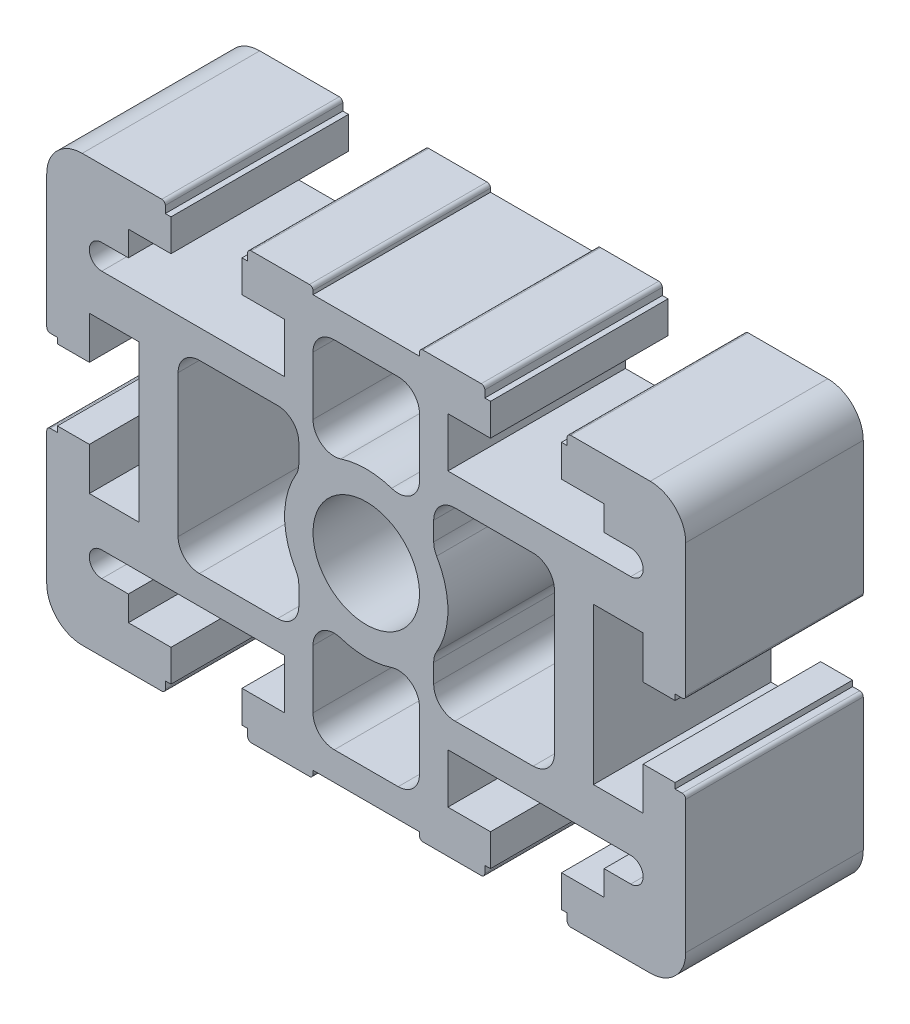
SolidWorks part; units mm, degrees
material "1060 Alloy"
ref_plane "Front" through (0, 0, 0) normal (0, 0, 1) x (1, 0, 0)
ref_plane "Top" through (0, 0, 0) normal (0, 1, 0) x (1, 0, 0)
ref_plane "Right" through (0, 0, 0) normal (1, 0, 0) x (0, 0, -1)
ref_plane "Plane1" through (0, 0, 0) normal (0, 0, 1) x (1, 0, 0)
sketch "Sketch1" plane through (0, 0, 0) normal (0, 0, 1) x (1, 0, 0)
  line L0 (7.4988, -13.7844) -> (7.4988, -22)
  line L1 (4.4988, -25) -> (-4.4988, -25)
  line L2 (-7.4988, -22) -> (-7.4988, -13.7844)
  line L3 (-7.4988, 13.7844) -> (-7.4988, 22)
  line L4 (-4.4988, 25) -> (4.4988, 25)
  line L5 (7.4988, 22) -> (7.4988, 13.7844)
  line L6 (26.4988, 10) -> (26.4988, -10)
  line L7 (23.4988, -13) -> (12.4988, -13)
  line L8 (9.4988, -10) -> (9.4988, -7.3505)
  line L9 (9.4988, 7.3505) -> (9.4988, 10)
  line L10 (12.4988, 13) -> (23.4988, 13)
  line L11 (-9.4988, -7.3505) -> (-9.4988, -10)
  line L12 (-12.4988, -13) -> (-23.4988, -13)
  line L13 (-26.4988, -10) -> (-26.4988, 10)
  line L14 (-23.4988, 13) -> (-12.4988, 13)
  line L15 (-9.4988, 10) -> (-9.4988, 7.3505)
  line L16 (28.7987, -30) -> (39.9987, -30)
  line L17 (44.9987, -25) -> (44.9987, -6.3)
  line L18 (44.4987, -5.8) -> (43.4987, -5.8)
  line L19 (43.4987, -5.8) -> (43.4987, -5)
  line L20 (43.4987, -5) -> (38.9987, -5)
  line L21 (38.9987, -5) -> (38.9987, -11)
  line L22 (38.9987, -11) -> (31.9987, -11)
  line L23 (31.9987, -11) -> (31.9987, 11)
  line L24 (31.9987, 11) -> (38.9987, 11)
  line L25 (38.9987, 11) -> (38.9987, 5)
  line L26 (38.9987, 5) -> (43.4987, 5)
  line L27 (43.4987, 5) -> (43.4987, 5.8)
  line L28 (43.4987, 5.8) -> (44.4987, 5.8)
  line L29 (44.9987, 6.3) -> (44.9987, 25)
  line L30 (39.9987, 30) -> (28.7987, 30)
  line L31 (28.2987, 29.5) -> (28.2987, 28.5)
  line L32 (28.2987, 28.5) -> (27.4987, 28.5)
  line L33 (27.4987, 28.5) -> (27.4987, 24)
  line L34 (27.4987, 24) -> (33.4987, 24)
  line L35 (33.4987, 24) -> (33.4987, 20.5)
  line L36 (33.4987, 20.5) -> (37.2511, 20.5)
  line L37 (37.2511, 17) -> (11.4988, 17)
  line L38 (11.4988, 17) -> (11.4988, 24)
  line L39 (11.4988, 24) -> (17.4988, 24)
  line L40 (17.4988, 24) -> (17.4988, 28.5)
  line L41 (17.4988, 28.5) -> (16.6988, 28.5)
  line L42 (16.6988, 28.5) -> (16.6988, 29.5)
  line L43 (16.1988, 30) -> (8, 30)
  line L44 (7.5, 29.5) -> (7.5, 29)
  line L45 (7.5, 29) -> (-7.5, 29)
  line L46 (-7.5, 29) -> (-7.5, 29.5)
  line L47 (-8, 30) -> (-16.1988, 30)
  line L48 (-16.6988, 29.5) -> (-16.6988, 28.5)
  line L49 (-16.6988, 28.5) -> (-17.4988, 28.5)
  line L50 (-17.4988, 28.5) -> (-17.4988, 24)
  line L51 (-17.4988, 24) -> (-11.4988, 24)
  line L52 (-11.4988, 24) -> (-11.4988, 17)
  line L53 (-11.4988, 17) -> (-37.2511, 17)
  line L54 (-37.2511, 20.5) -> (-33.4987, 20.5)
  line L55 (-33.4987, 20.5) -> (-33.4987, 24)
  line L56 (-33.4987, 24) -> (-27.4987, 24)
  line L57 (-27.4987, 24) -> (-27.4987, 28.5)
  line L58 (-27.4987, 28.5) -> (-28.2987, 28.5)
  line L59 (-28.2987, 28.5) -> (-28.2987, 29.5)
  line L60 (-28.7987, 30) -> (-39.9987, 30)
  line L61 (-44.9987, 25) -> (-44.9987, 6.3)
  line L62 (-44.4987, 5.8) -> (-43.4987, 5.8)
  line L63 (-43.4987, 5.8) -> (-43.4987, 5)
  line L64 (-43.4987, 5) -> (-38.9987, 5)
  line L65 (-38.9987, 5) -> (-38.9987, 11)
  line L66 (-38.9987, 11) -> (-31.9987, 11)
  line L67 (-31.9987, 11) -> (-31.9987, -11)
  line L68 (-31.9987, -11) -> (-38.9987, -11)
  line L69 (-38.9987, -11) -> (-38.9987, -5)
  line L70 (-38.9987, -5) -> (-43.4987, -5)
  line L71 (-43.4987, -5) -> (-43.4987, -5.8)
  line L72 (-43.4987, -5.8) -> (-44.4987, -5.8)
  line L73 (-44.9987, -6.3) -> (-44.9987, -25)
  line L74 (-39.9987, -30) -> (-28.7987, -30)
  line L75 (-28.2987, -29.5) -> (-28.2987, -28.5)
  line L76 (-28.2987, -28.5) -> (-27.4987, -28.5)
  line L77 (-27.4987, -28.5) -> (-27.4987, -24)
  line L78 (-27.4987, -24) -> (-33.4987, -24)
  line L79 (-33.4987, -24) -> (-33.4987, -20.5)
  line L80 (-33.4987, -20.5) -> (-37.2511, -20.5)
  line L81 (-37.2511, -17) -> (-11.4988, -17)
  line L82 (-11.4988, -17) -> (-11.4988, -24)
  line L83 (-11.4988, -24) -> (-17.4988, -24)
  line L84 (-17.4988, -24) -> (-17.4988, -28.5)
  line L85 (-17.4988, -28.5) -> (-16.6988, -28.5)
  line L86 (-16.6988, -28.5) -> (-16.6988, -29.5)
  line L87 (-16.1988, -30) -> (-8, -30)
  line L88 (-7.5, -29.5) -> (-7.5, -29)
  line L89 (-7.5, -29) -> (7.5, -29)
  line L90 (7.5, -29) -> (7.5, -29.5)
  line L91 (8, -30) -> (16.1988, -30)
  line L92 (16.6988, -29.5) -> (16.6988, -28.5)
  line L93 (16.6988, -28.5) -> (17.4988, -28.5)
  line L94 (17.4988, -28.5) -> (17.4988, -24)
  line L95 (17.4988, -24) -> (11.4988, -24)
  line L96 (11.4988, -24) -> (11.4988, -17)
  line L97 (11.4988, -17) -> (37.2511, -17)
  line L98 (37.2511, -20.5) -> (33.4987, -20.5)
  line L99 (33.4987, -20.5) -> (33.4987, -24)
  line L100 (33.4987, -24) -> (27.4987, -24)
  line L101 (27.4987, -24) -> (27.4987, -28.5)
  line L102 (27.4987, -28.5) -> (28.2987, -28.5)
  line L103 (28.2987, -28.5) -> (28.2987, -29.5)
  circle A0 centre (0, 0) radius 7.5
  arc A1 (3.568, -10.9325) -> (7.4988, -13.7844) centre (4.4988, -13.7844) cw
  arc A2 (7.4988, -22) -> (4.4988, -25) centre (4.4988, -22) cw
  arc A3 (-4.4988, -25) -> (-7.4988, -22) centre (-4.4988, -22) cw
  arc A4 (-7.4988, -13.7844) -> (-3.568, -10.9325) centre (-4.4988, -13.7844) cw
  arc A5 (-3.568, -10.9325) -> (3.568, -10.9325) centre (0, 0) ccw
  arc A6 (-3.568, 10.9325) -> (-7.4988, 13.7844) centre (-4.4988, 13.7844) cw
  arc A7 (-7.4988, 22) -> (-4.4988, 25) centre (-4.4988, 22) cw
  arc A8 (4.4988, 25) -> (7.4988, 22) centre (4.4988, 22) cw
  arc A9 (7.4988, 13.7844) -> (3.568, 10.9325) centre (4.4988, 13.7844) cw
  arc A10 (3.568, 10.9325) -> (-3.568, 10.9325) centre (0, 0) ccw
  arc A11 (26.4988, -10) -> (23.4988, -13) centre (23.4988, -10) cw
  arc A12 (12.4988, -13) -> (9.4988, -10) centre (12.4988, -10) cw
  arc A13 (9.4988, -7.3505) -> (9.9128, -5.8297) centre (12.4988, -7.3505) cw
  arc A14 (9.9128, -5.8297) -> (9.9128, 5.8297) centre (0, 0) ccw
  arc A15 (9.9128, 5.8297) -> (9.4988, 7.3505) centre (12.4988, 7.3505) cw
  arc A16 (9.4988, 10) -> (12.4988, 13) centre (12.4988, 10) cw
  arc A17 (23.4988, 13) -> (26.4988, 10) centre (23.4988, 10) cw
  arc A18 (-9.9128, -5.8297) -> (-9.4988, -7.3505) centre (-12.4988, -7.3505) cw
  arc A19 (-9.4988, -10) -> (-12.4988, -13) centre (-12.4988, -10) cw
  arc A20 (-23.4988, -13) -> (-26.4988, -10) centre (-23.4988, -10) cw
  arc A21 (-26.4988, 10) -> (-23.4988, 13) centre (-23.4988, 10) cw
  arc A22 (-12.4988, 13) -> (-9.4988, 10) centre (-12.4988, 10) cw
  arc A23 (-9.4988, 7.3505) -> (-9.9128, 5.8297) centre (-12.4988, 7.3505) cw
  arc A24 (-9.9128, 5.8297) -> (-9.9128, -5.8297) centre (0, 0) ccw
  arc A25 (28.2987, -29.5) -> (28.7987, -30) centre (28.7987, -29.5) ccw
  arc A26 (39.9987, -30) -> (44.9987, -25) centre (39.9987, -25) ccw
  arc A27 (44.9987, -6.3) -> (44.4987, -5.8) centre (44.4987, -6.3) ccw
  arc A28 (44.4987, 5.8) -> (44.9987, 6.3) centre (44.4987, 6.3) ccw
  arc A29 (44.9987, 25) -> (39.9987, 30) centre (39.9987, 25) ccw
  arc A30 (28.7987, 30) -> (28.2987, 29.5) centre (28.7987, 29.5) ccw
  arc A31 (37.2511, 20.5) -> (37.2511, 17) centre (37.2511, 18.75) cw
  arc A32 (16.6988, 29.5) -> (16.1988, 30) centre (16.1988, 29.5) ccw
  arc A33 (8, 30) -> (7.5, 29.5) centre (8, 29.5) ccw
  arc A34 (-7.5, 29.5) -> (-8, 30) centre (-8, 29.5) ccw
  arc A35 (-16.1988, 30) -> (-16.6988, 29.5) centre (-16.1988, 29.5) ccw
  arc A36 (-37.2511, 17) -> (-37.2511, 20.5) centre (-37.2511, 18.75) cw
  arc A37 (-28.2987, 29.5) -> (-28.7987, 30) centre (-28.7987, 29.5) ccw
  arc A38 (-39.9987, 30) -> (-44.9987, 25) centre (-39.9987, 25) ccw
  arc A39 (-44.9987, 6.3) -> (-44.4987, 5.8) centre (-44.4987, 6.3) ccw
  arc A40 (-44.4987, -5.8) -> (-44.9987, -6.3) centre (-44.4987, -6.3) ccw
  arc A41 (-44.9987, -25) -> (-39.9987, -30) centre (-39.9987, -25) ccw
  arc A42 (-28.7987, -30) -> (-28.2987, -29.5) centre (-28.7987, -29.5) ccw
  arc A43 (-37.2511, -20.5) -> (-37.2511, -17) centre (-37.2511, -18.75) cw
  arc A44 (-16.6988, -29.5) -> (-16.1988, -30) centre (-16.1988, -29.5) ccw
  arc A45 (-8, -30) -> (-7.5, -29.5) centre (-8, -29.5) ccw
  arc A46 (7.5, -29.5) -> (8, -30) centre (8, -29.5) ccw
  arc A47 (16.1988, -30) -> (16.6988, -29.5) centre (16.1988, -29.5) ccw
  arc A48 (37.2511, -17) -> (37.2511, -20.5) centre (37.2511, -18.75) cw
extrude "Boss-Extrude1" add sketch "Sketch1" against normal blind 25
